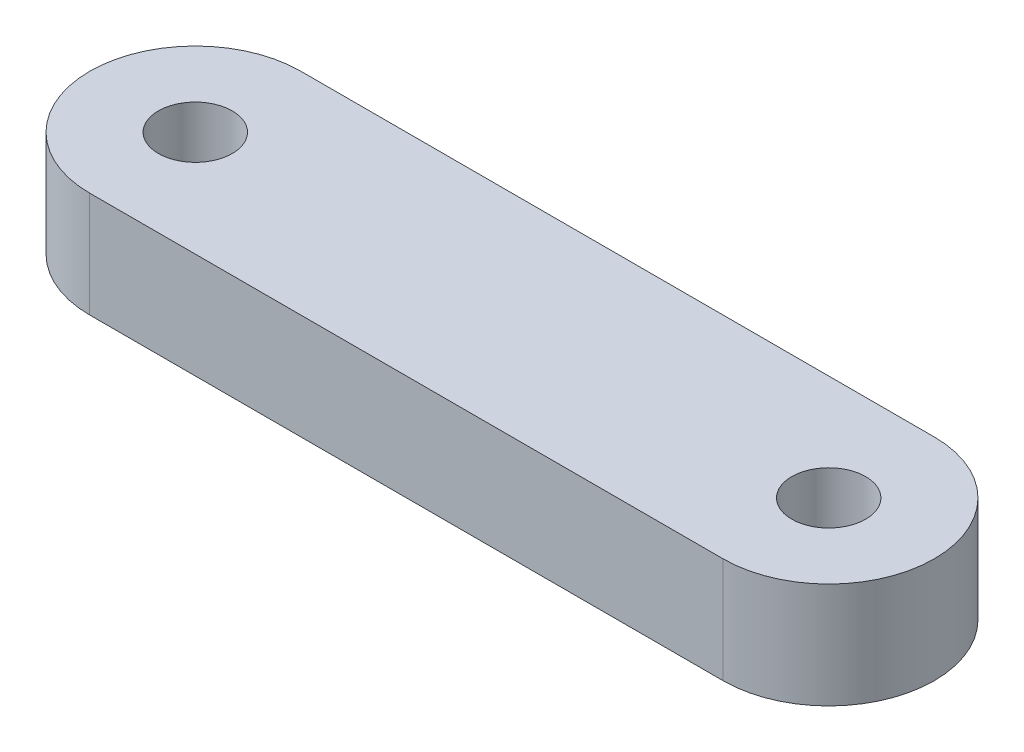
SolidWorks part; units mm, degrees
material "Balsa"
ref_plane "Front Plane" through (0, 0, 0) normal (0, 0, 1) x (1, 0, 0)
ref_plane "Top Plane" through (0, 0, 0) normal (0, 1, 0) x (1, 0, 0)
ref_plane "Right Plane" through (0, 0, 0) normal (1, 0, 0) x (0, 0, -1)
sketch "Sketch1" plane through (0, 0, 0) normal (0, 1, 0) x (1, 0, 0)
  line L0 (0, 0) -> (30, 0)
  line L2 (30, 10) -> (0, 10)
  arc A0 (0, 10) -> (0, 0) centre (0, 5) ccw
  arc A1 (30, 10) -> (30, 0) centre (30, 5) cw
  circle A2 centre (0, 5) radius 1.75
  circle A3 centre (30, 5) radius 1.75
  dimension "D1" = 3.5
  dimension "D2" = 30
  dimension "D3" = 10
extrude "Boss-Extrude1" add sketch "Sketch1" along normal blind 5
